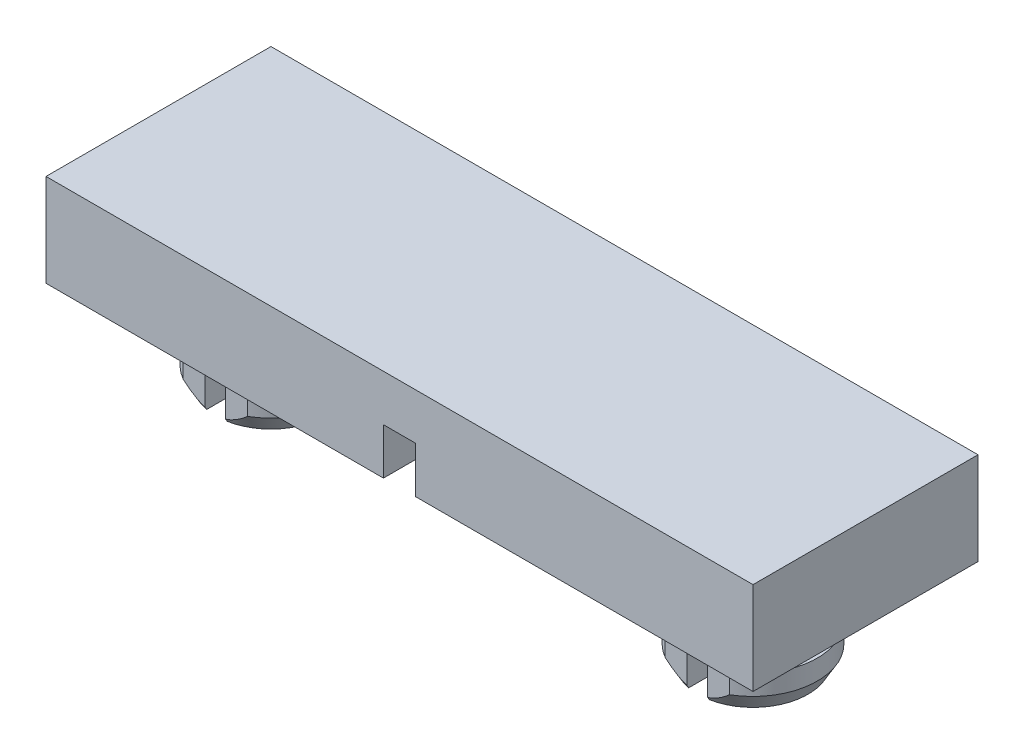
SolidWorks part; units mm, degrees
ref_plane "Front Plane" through (0, 0, 0) normal (0, 0, 1) x (1, 0, 0)
ref_plane "Top Plane" through (0, 0, 0) normal (0, 1, 0) x (1, 0, 0)
ref_plane "Right Plane" through (0, 0, 0) normal (1, 0, 0) x (0, 0, -1)
sketch "Sketch1" plane through (0, 0, 0) normal (0, 1, 0) x (1, 0, 0)
  line L1 (0, 0) -> (34.925, 0)
  line L2 (0, 0) -> (0, 11.1125)
  line L3 (0, 11.1125) -> (34.925, 11.1125)
  line L4 (34.925, 0) -> (34.925, 11.1125)
  dimension "D1" = 34.925
  dimension "D2" = 11.1125
extrude "Boss-Extrude1" add sketch "Sketch1" along normal blind 4.572
sketch "Sketch2" plane through (0, 0, 0) normal (0, -1, 0) x (1, 0, 0)
  line L0 (0, -5.5562) -> (34.925, -5.5562) construction
  line L1 (0, -11.1125) -> (0, 0) construction
  line L2 (34.925, 0) -> (34.925, -11.1125) construction
  line L3 (17.4625, 0) -> (17.4625, -11.1125) construction
  line L4 (0, 0) -> (34.925, 0) construction
  line L5 (34.925, -11.1125) -> (0, -11.1125) construction
  line L7 (16.6687, 0) -> (18.2562, 0)
  line L8 (16.6687, 0) -> (16.6688, -11.1125)
  line L9 (16.6688, -11.1125) -> (18.2562, -11.1125)
  line L10 (18.2562, 0) -> (18.2562, -11.1125)
  dimension "D1" = 1.5875
extrude "Cut-Extrude1" cut sketch "Sketch2" against normal blind 2.286
sketch "Sketch3" plane through (0, 0, 0) normal (0, -1, 0) x (1, 0, 0)
  line L0 (34.925, -5.5562) -> (0, -5.5562) construction
  line L1 (34.925, 0) -> (34.925, -11.1125) construction
  line L2 (0, -11.1125) -> (0, 0) construction
  line L3 (29.3687, 0) -> (29.3687, -11.1125) construction
  line L4 (18.2562, 0) -> (34.925, 0) construction
  line L5 (34.925, -11.1125) -> (18.2562, -11.1125) construction
  line L6 (5.5562, 0) -> (5.5562, -11.1125) construction
  line L7 (0, 0) -> (16.6687, 0) construction
  line L8 (16.6688, -11.1125) -> (0, -11.1125) construction
  line L9 (5.0482, -2.8088) -> (5.0482, -8.3037)
  line L10 (6.0642, -2.8088) -> (6.0642, -8.3037)
  line L11 (28.8607, -2.8088) -> (28.8607, -8.3037)
  line L12 (29.8768, -2.8088) -> (29.8768, -8.3037)
  arc A0 (5.0482, -2.8088) -> (5.0482, -8.3037) centre (5.5562, -5.5562) ccw
  arc A1 (28.8607, -2.8088) -> (28.8607, -8.3037) centre (29.3687, -5.5562) ccw
  arc A2 (6.0642, -8.3037) -> (6.0642, -2.8088) centre (5.5562, -5.5562) ccw
  arc A3 (29.8768, -8.3037) -> (29.8768, -2.8088) centre (29.3687, -5.5562) ccw
  dimension "D3" = 2.794
  dimension "D1" = 5.5562
  dimension "D2" = 5.5562
  dimension "D4" = 1.016
  dimension "D5" = 1.016
extrude "Boss-Extrude2" add sketch "Sketch3" along normal blind 2.54
sketch "Sketch4" plane through (0, -2.54, 0) normal (0, -1, 0) x (1, 0, 0)
  line L0 (5.0482, -2.8088) -> (5.0482, -8.3037)
  line L1 (6.0642, -2.8088) -> (6.0642, -8.3037) construction
  line L3 (5.0482, -8.3037) -> (5.0482, -2.8088) construction
  line L4 (6.0642, -2.8088) -> (6.0642, -8.3037)
  line L5 (6.0642, -2.8088) -> (7.1476, -2.8088)
  line L6 (6.0642, -8.3037) -> (7.1476, -8.3037)
  line L7 (3.9649, -2.8088) -> (5.0482, -2.8088)
  line L8 (28.8607, -2.8088) -> (27.7774, -2.8088)
  line L9 (29.8768, -2.8088) -> (30.9601, -2.8088)
  line L10 (29.8768, -2.8088) -> (29.8768, -8.3037) construction
  line L11 (3.9649, -8.3037) -> (5.0482, -8.3037)
  line L12 (29.8768, -8.3037) -> (30.9601, -8.3037)
  line L13 (28.8607, -8.3037) -> (27.7774, -8.3037)
  line L14 (28.8607, -2.8088) -> (28.8607, -8.3037)
  line L15 (29.8768, -2.8088) -> (29.8768, -8.3037)
  arc A0 (30.9601, -8.3037) -> (30.9601, -2.8088) centre (29.3687, -5.5562) ccw
  arc A1 (27.7774, -2.8088) -> (27.7774, -8.3037) centre (29.3687, -5.5562) ccw
  arc A2 (7.1476, -8.3037) -> (7.1476, -2.8088) centre (5.5562, -5.5562) ccw
  arc A3 (3.9649, -2.8088) -> (3.9649, -8.3037) centre (5.5562, -5.5562) ccw
  dimension "D1" = 3.175
  dimension "D2" = 3.175
extrude "Boss-Extrude3" add sketch "Sketch4" along normal blind 1.778
chamfer "Chamfer1" distance 0.7937 angle 30 4 edges at (32.5437, -4.318, -5.5562) (26.1938, -4.318, -5.5562) (2.3812, -4.318, -5.5562) (8.7312, -4.318, -5.5562)
